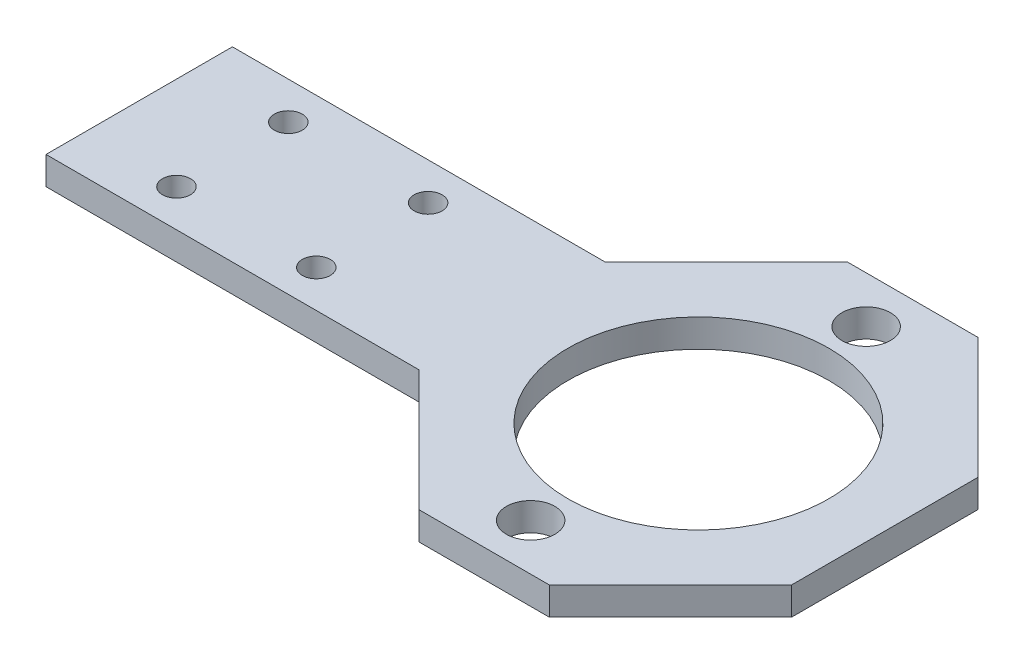
SolidWorks part; units mm, degrees
material "Thornel Mat VMA"
ref_plane "前视基准面" through (0, 0, 0) normal (0, 0, 1) x (1, 0, 0)
ref_plane "上视基准面" through (0, 0, 0) normal (0, 1, 0) x (1, 0, 0)
ref_plane "右视基准面" through (0, 0, 0) normal (1, 0, 0) x (0, 0, -1)
sketch "草图1" plane through (0, 0, 0) normal (0, 1, 0) x (1, 0, 0)
  line L1 (-60, 10) -> (-20, 10)
  line L2 (-60, 10) -> (-60, -10)
  line L3 (-60, -10) -> (-20, -10)
  line L6 (0, 0) -> (18, 0) construction
  line L9 (0, 18) -> (0, -18) construction
  line L10 (-50, 6) -> (-35, 6) construction
  line L11 (-50, 6) -> (-50, -6) construction
  line L12 (-50, -6) -> (-35, -6) construction
  line L13 (-35, 6) -> (-35, -6) construction
  line L14 (-20, 10) -> (-7, 23)
  line L15 (-7, 23) -> (7, 23)
  line L16 (7, 23) -> (20, 10)
  line L17 (20, 10) -> (20, -10)
  line L18 (20, -10) -> (7, -23)
  line L19 (7, -23) -> (-7, -23)
  line L20 (-7, -23) -> (-20, -10)
  line L21 (-60, 0) -> (20, 0) construction
  line L22 (-20, 10) -> (-20, -10) construction
  circle A0 centre (-35, 6) radius 1.5
  circle A1 centre (-50, 6) radius 1.5
  circle A2 centre (-35, -6) radius 1.5
  circle A3 centre (-50, -6) radius 1.5
  circle A4 centre (0, 0) radius 14
  circle A5 centre (0, 18) radius 2.6
  circle A6 centre (0, -18) radius 2.6
  point P24 (0, 18)
  point P26 (-3.8669, -17.5797)
  point P30 (0, 0)
  point P32 (-50.1032, -6)
  dimension "D2" = 25
  dimension "D3" = 4
  dimension "D4" = 15
  dimension "D5" = 12
  dimension "D6" = 60
  dimension "D7" = 28
  dimension "D9" = 18
  dimension "D12" = 45
  dimension "D13" = 3
  dimension "D14" = 5.2
  dimension "D18" = 20
  dimension "D1" = 20
  dimension "D8" = 18
  dimension "D11" = 18
  dimension "D15" = 45
  dimension "D16" = 45
  dimension "D17" = 45
  dimension "D19" = 20
  dimension "D20" = 23
extrude "凸台-拉伸1" add sketch "草图1" along normal blind 3
